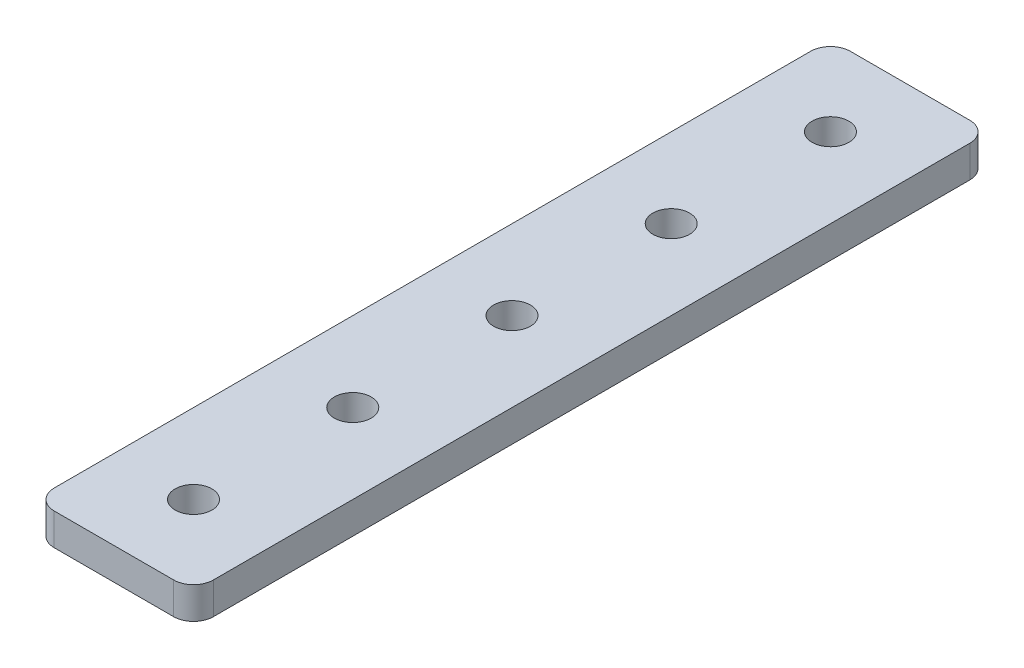
SolidWorks part; units mm, degrees
ref_plane "Front Plane" through (0, 0, 0) normal (0, 0, 1) x (1, 0, 0)
ref_plane "Top Plane" through (0, 0, 0) normal (0, 1, 0) x (1, 0, 0)
ref_plane "Right Plane" through (0, 0, 0) normal (1, 0, 0) x (0, 0, -1)
ref_plane "Plane1" through (0, 3.2, 0) normal (0, 1, 0) x (1, 0, 0)
sketch "Sketch1" plane through (0, 3.2, 0) normal (0, 1, 0) x (1, 0, 0)
  line L0 (8, 2) -> (8, 286)
  line L1 (6, 288) -> (-6, 288)
  line L2 (-8, 286) -> (-8, 2)
  line L3 (-6, 0) -> (6, 0)
  circle A0 centre (0, 280) radius 1.85
  circle A1 centre (0, 264) radius 1.85
  circle A2 centre (0, 248) radius 1.85
  circle A3 centre (0, 232) radius 1.85
  circle A4 centre (0, 216) radius 1.85
  circle A5 centre (0, 200) radius 1.85
  circle A6 centre (0, 184) radius 1.85
  circle A7 centre (0, 168) radius 1.85
  circle A8 centre (0, 152) radius 1.85
  circle A9 centre (0, 136) radius 1.85
  circle A10 centre (0, 120) radius 1.85
  circle A11 centre (0, 104) radius 1.85
  circle A12 centre (0, 88) radius 1.85
  circle A13 centre (0, 72) radius 1.85
  circle A14 centre (0, 56) radius 1.85
  circle A15 centre (0, 40) radius 1.85
  circle A16 centre (0, 24) radius 1.85
  circle A17 centre (0, 8) radius 1.85
  arc A18 (8, 286) -> (6, 288) centre (6, 286) ccw
  arc A19 (-6, 288) -> (-8, 286) centre (-6, 286) ccw
  arc A20 (-8, 2) -> (-6, 0) centre (-6, 2) ccw
  arc A21 (6, 0) -> (8, 2) centre (6, 2) ccw
extrude "Boss-Extrude1" add sketch "Sketch1" against normal blind 3.2
sketch "Sketch2" plane through (0, 0, 0) normal (0, 1, 0) x (1, 0, 0)
  line L0 (-38.6468, 80) -> (26.4425, 80)
  circle A0 centre (0, 72) radius 1.85 construction
  dimension "D1" = 8
extrude "Cut-Extrude1" cut sketch "Sketch2" against normal through all both and the other way through all
fillet "Fillet1" radius 2 2 edges at (8, 1.6, -80) (-8, 1.6, -80)
